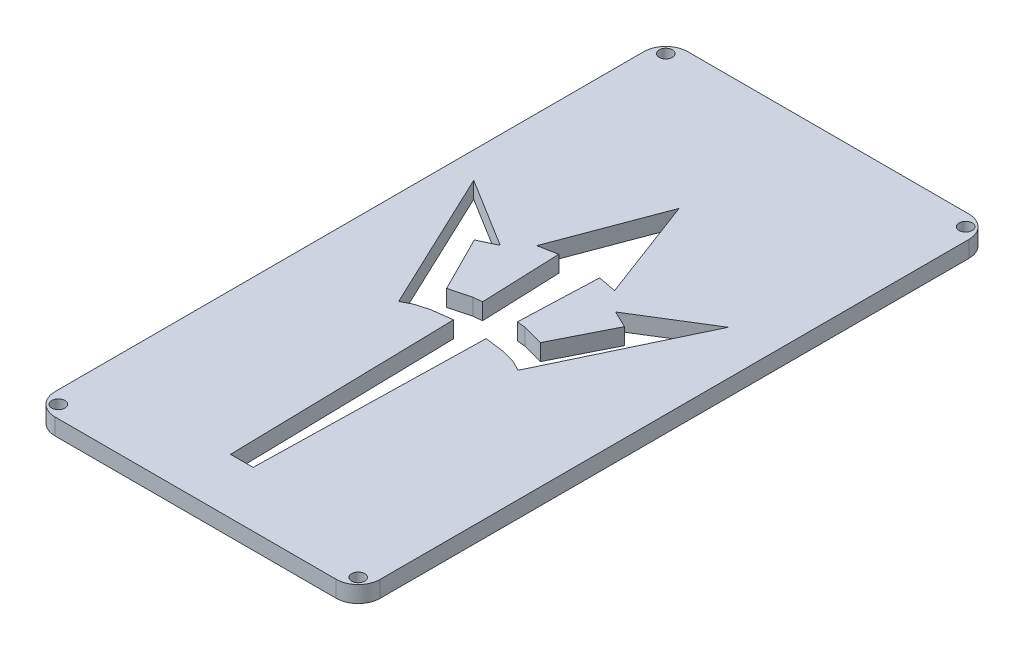
SolidWorks part; units mm, degrees
ref_plane "Front Plane" through (0, 0, 0) normal (0, 0, 1) x (1, 0, 0)
ref_plane "Top Plane" through (0, 0, 0) normal (0, 1, 0) x (1, 0, 0)
ref_plane "Right Plane" through (0, 0, 0) normal (1, 0, 0) x (0, 0, -1)
sketch "Sketch1" plane through (0, 0, 0) normal (0, 1, 0) x (1, 0, 0)
  line L0 (6.35, 180.34) -> (87.63, 180.34) construction
  line L1 (6.35, 0) -> (87.63, 0)
  line L2 (0, 6.35) -> (0, 176.53)
  line L3 (6.35, 182.88) -> (87.63, 182.88)
  line L4 (93.98, 6.35) -> (93.98, 176.53)
  line L5 (91.44, 6.35) -> (91.44, 176.53) construction
  line L6 (6.35, 2.54) -> (87.63, 2.54) construction
  line L7 (2.54, 6.35) -> (2.54, 176.53) construction
  arc A0 (6.35, 0) -> (0, 6.35) centre (6.35, 6.35) cw
  arc A1 (87.63, 0) -> (93.98, 6.35) centre (87.63, 6.35) ccw
  arc A2 (87.63, 182.88) -> (93.98, 176.53) centre (87.63, 176.53) cw
  arc A3 (0, 176.53) -> (6.35, 182.88) centre (6.35, 176.53) cw
  arc A5 (87.63, 180.34) -> (91.44, 176.53) centre (87.63, 176.53) cw construction
  arc A6 (87.63, 2.54) -> (91.44, 6.35) centre (87.63, 6.35) ccw construction
  arc A7 (6.35, 2.54) -> (2.54, 6.35) centre (6.35, 6.35) cw construction
  arc A8 (2.54, 176.53) -> (6.35, 180.34) centre (6.35, 176.53) cw construction
  circle A9 centre (3.6559, 179.2241) radius 1.905
  circle A10 centre (90.3241, 179.2241) radius 1.905
  circle A11 centre (3.6559, 3.6559) radius 1.905
  circle A12 centre (90.3241, 3.6559) radius 1.905
  point P7 (0, 0)
  dimension "D3" = 6.35
  dimension "D4" = 3.81
  dimension "D6" = 3.81
  dimension "D7" = 3.81
  dimension "D8" = 3.81
  dimension "D1" = 93.98
  dimension "D2" = 182.88
  dimension "D5" = 2.54
sketch "Sketch2" plane through (0, 0, 0) normal (0, 1, 0) x (1, 0, 0)
  line L0 (44.3309, 142.4124) -> (55.5833, 112.4856)
  line L1 (55.5833, 112.4856) -> (50.2364, 113.5231)
  line L2 (50.2364, 113.5231) -> (49.3586, 90.6191)
  line L3 (49.3586, 90.6191) -> (51.8924, 90.3597)
  line L4 (51.8924, 90.3597) -> (57.8977, 88.7836)
  line L5 (57.8977, 88.7836) -> (66.0378, 104.9042)
  line L6 (66.0378, 104.9042) -> (61.09, 107.2983)
  line L7 (61.09, 107.2983) -> (81.2008, 119.7479)
  line L8 (81.2008, 119.7479) -> (61.5687, 78.5685)
  line L9 (61.5687, 78.5685) -> (58.8653, 80.005)
  line L10 (58.8653, 80.005) -> (55.0035, 81.1272)
  line L11 (55.0035, 81.1272) -> (49.0394, 81.9203)
  line L12 (49.0394, 81.9203) -> (47.6029, 16.0014)
  line L13 (47.6029, 16.0014) -> (44.3309, 16.0014)
  line L14 (44.3309, 16.0014) -> (41.0582, 16.0014)
  line L15 (41.0582, 16.0014) -> (39.6217, 81.9203)
  line L16 (39.6217, 81.9203) -> (33.6913, 81.1273)
  line L17 (33.6913, 81.1273) -> (29.8257, 80.005)
  line L18 (29.8257, 80.005) -> (27.0924, 78.5685)
  line L19 (27.0924, 78.5685) -> (7.62, 119.7479)
  line L20 (7.62, 119.7479) -> (27.7308, 107.2983)
  line L21 (27.7308, 107.2983) -> (22.6233, 104.9042)
  line L22 (22.6233, 104.9042) -> (30.7634, 88.7836)
  line L23 (30.7634, 88.7836) -> (36.7388, 90.3597)
  line L24 (36.7388, 90.3597) -> (39.3025, 90.6191)
  line L25 (39.3025, 90.6191) -> (38.4247, 113.5231)
  line L26 (38.4247, 113.5231) -> (33.0778, 112.4856)
  line L27 (33.0778, 112.4856) -> (44.3309, 142.4124)
extrude "Boss-Extrude1" add sketch "Sketch1" along normal blind 4.7625 contours A3 L2 A0 L1 A1 L4 A2 L3 A12 A11 A10 A9
extrude "Cut-Extrude3" cut sketch "Sketch2" along normal through all contours L16 L17 L18 L19 L20 L21 L22 L23 L24 L25 L26 L27 L0 L1 L2 L3 L4 L5 L6 L7 L8 L9 L10 L11 L12 L13 L14 L15
sketch "Sketch3" plane through (0, 0, 0) normal (0, 1, 0) x (1, 0, 0)
  line L0 (16.9105, 182.88) -> (16.9105, 180.34)
  line L1 (6.35, 182.88) -> (87.63, 182.88) construction
  line L2 (16.9105, 180.34) -> (74.451, 180.34)
  line L3 (74.451, 180.34) -> (74.451, 182.88)
  arc A0 (6.35, 182.88) -> (0, 176.53) centre (6.35, 176.53) ccw construction
  point P4 (16.9105, 181.61)
  point P10 (1.8599, 181.0201)
  dimension "D1" = 2.54
  dimension "D2" = 15.0622
